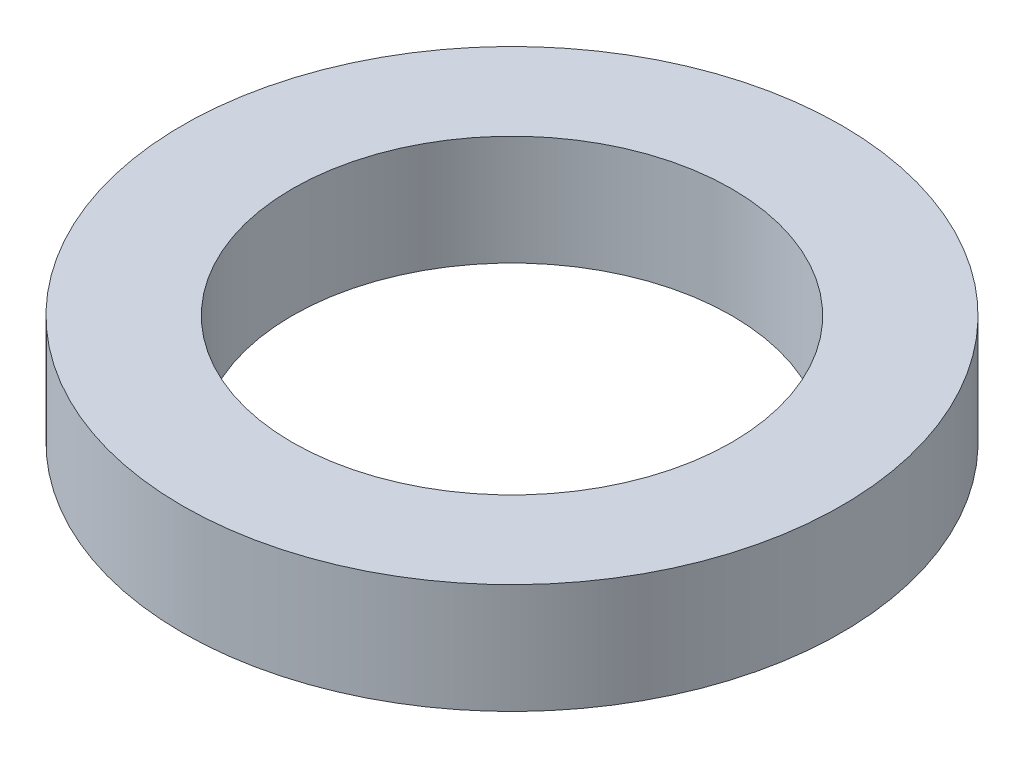
SolidWorks part; units mm, degrees
ref_plane "Front Plane" through (0, 0, 0) normal (0, 0, 1) x (1, 0, 0)
ref_plane "Top Plane" through (0, 0, 0) normal (0, 1, 0) x (1, 0, 0)
ref_plane "Right Plane" through (0, 0, 0) normal (1, 0, 0) x (0, 0, -1)
sketch "Sketch1" plane through (0, 0, 0) normal (0, 1, 0) x (1, 0, 0)
  circle A0 centre (0, 0) radius 9.525
  dimension "OD" = 19.05
extrude "Boss-Extrude1" add sketch "Sketch1" along normal blind 3.175
sketch "Sketch5" plane through (0, 3.175, 0) normal (0, 1, 0) x (-1, 0, 0)
  circle A0 centre (0, 0) radius 6.35
  dimension "ID" = 12.7
extrude "Cut-Extrude1" cut sketch "Sketch5" against normal through all
